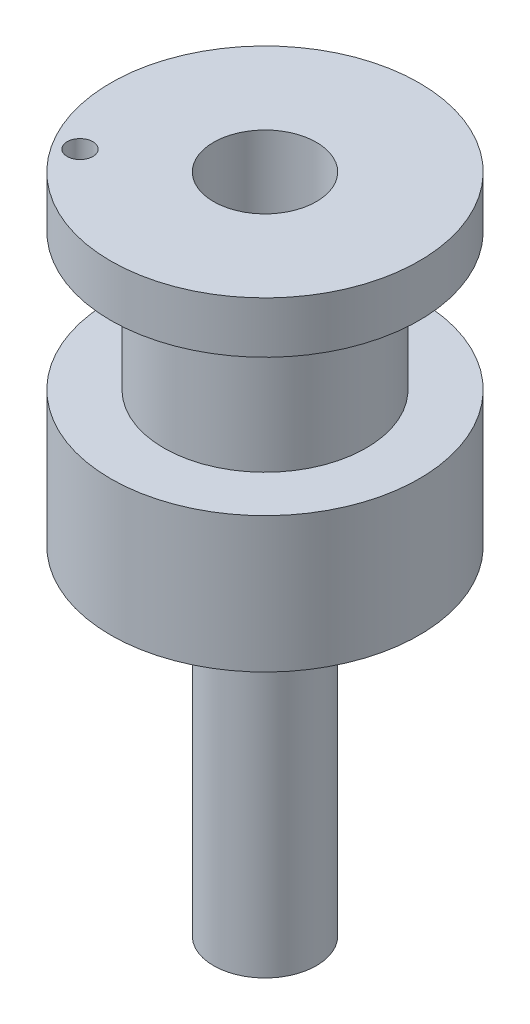
SolidWorks part; units mm, degrees
material "1060 Alloy"
ref_plane "Front Plane" through (0, 0, 0) normal (0, 0, 1) x (1, 0, 0)
ref_plane "Top Plane" through (0, 0, 0) normal (0, 1, 0) x (1, 0, 0)
ref_plane "Right Plane" through (0, 0, 0) normal (1, 0, 0) x (0, 0, -1)
sketch "Sketch1" plane through (0, 0, 0) normal (0, 1, 0) x (1, 0, 0)
  circle A0 centre (0, 0) radius 3
  dimension "D1" = 6
extrude "Boss-Extrude1" add sketch "Sketch1" along normal blind 19.7
sketch "Sketch2" plane through (0, 19.7, 0) normal (0, 1, 0) x (1, 0, 0)
  circle A0 centre (0, 0) radius 9
  dimension "D1" = 18
extrude "Boss-Extrude2" add sketch "Sketch2" along normal blind 7.9
sketch "Sketch3" plane through (0, 27.6, 0) normal (0, 1, 0) x (1, 0, 0)
  circle A0 centre (0, 0) radius 5.9
  dimension "D1" = 11.8
extrude "Boss-Extrude3" add sketch "Sketch3" along normal blind 8
sketch "Sketch4" plane through (0, 35.6, 0) normal (0, 1, 0) x (1, 0, 0)
  circle A0 centre (0, 0) radius 9
extrude "Boss-Extrude4" add sketch "Sketch4" along normal blind 3
sketch "Sketch5" plane through (0, 38.6, 0) normal (0, 1, 0) x (1, 0, 0)
  circle A0 centre (0, 0) radius 3
  dimension "D1" = 6
extrude "Cut-Extrude1" cut sketch "Sketch5" against normal blind 9.6
sketch "Sketch7" plane through (0, 38.6, 0) normal (0, 1, 0) x (1, 0, 0)
  circle A0 centre (-6.551, -4.24) radius 0.75
  dimension "D1" = 1.5
extrude "Cut-Extrude2" cut sketch "Sketch7" against normal blind 10
